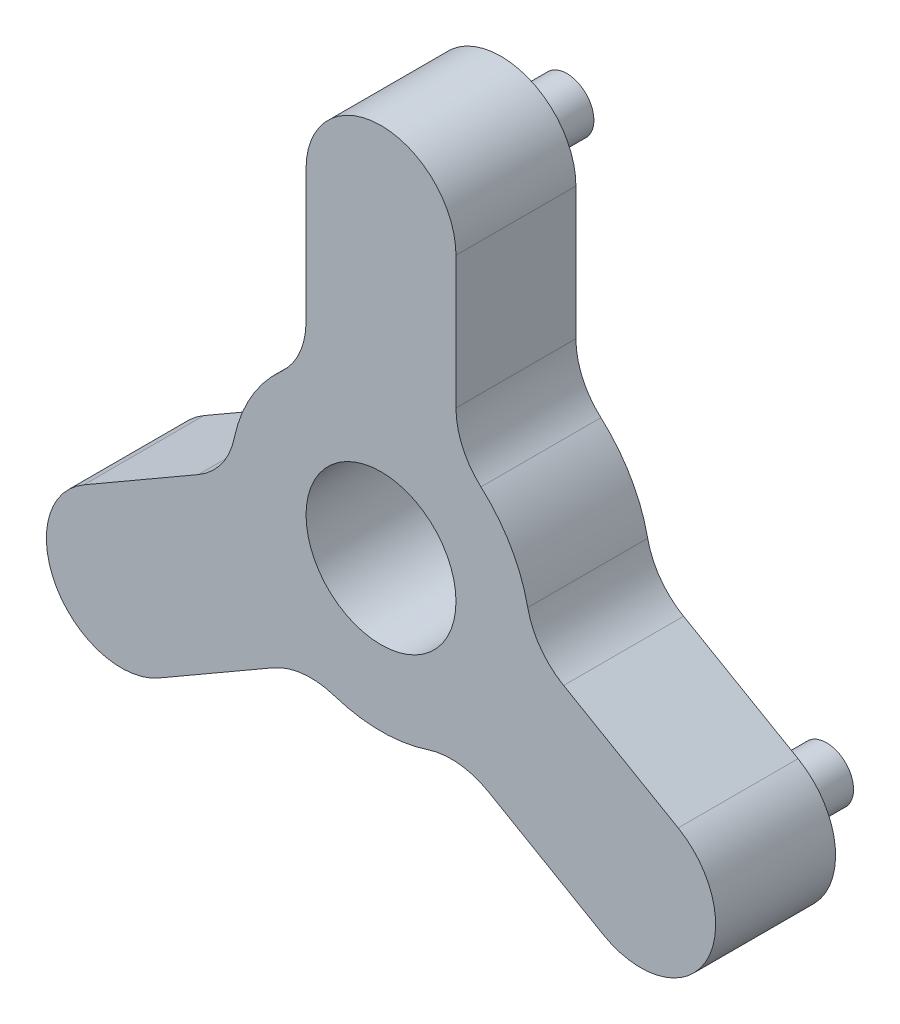
SolidWorks part; units mm, degrees
ref_plane "Front Plane" through (0, 0, 0) normal (0, 0, 1) x (1, 0, 0)
ref_plane "Top Plane" through (0, 0, 0) normal (0, 1, 0) x (1, 0, 0)
ref_plane "Right Plane" through (0, 0, 0) normal (1, 0, 0) x (0, 0, -1)
sketch "Sketch1" plane through (0, 0, 0) normal (0, 0, 1) x (1, 0, 0)
  line L0 (-6.35, 25.4) -> (-6.35, 14.199)
  line L1 (6.35, 25.4) -> (6.35, 14.199)
  line L10 (18.822, -18.1993) -> (9.1217, -12.5988)
  line L11 (25.172, -7.2007) -> (15.4717, -1.6003)
  line L12 (-25.172, -7.2007) -> (-15.4717, -1.6003)
  line L13 (-18.822, -18.1993) -> (-9.1217, -12.5988)
  circle A0 centre (0, 0) radius 25.4 construction
  circle A1 centre (0, 25.4) radius 2.2857 construction
  circle A3 centre (21.997, -12.7) radius 2.2857 construction
  arc A4 (18.822, -18.1993) -> (25.172, -7.2007) centre (21.997, -12.7) ccw
  circle A5 centre (-21.997, -12.7) radius 2.2857 construction
  arc A6 (-25.172, -7.2007) -> (-18.822, -18.1993) centre (-21.997, -12.7) ccw
  arc A7 (6.35, 25.4) -> (-6.35, 25.4) centre (0, 25.4) ccw
  arc A8 (12.4311, 2.5993) -> (8.4667, 9.466) centre (0, 0) ccw
  arc A9 (-3.9645, -12.0654) -> (3.9645, -12.0654) centre (0, 0) ccw
  arc A10 (-8.4667, 9.466) -> (-12.4311, 2.5993) centre (0, 0) ccw
  arc A11 (9.1217, -12.5988) -> (3.9645, -12.0654) centre (5.9467, -18.098) ccw
  arc A12 (-9.1217, -12.5988) -> (-3.9645, -12.0654) centre (-5.9467, -18.098) cw
  arc A13 (-15.4717, -1.6003) -> (-12.4311, 2.5993) centre (-18.6467, 3.899) ccw
  arc A14 (-6.35, 14.199) -> (-8.4667, 9.466) centre (-12.7, 14.199) cw
  arc A15 (6.35, 14.199) -> (8.4667, 9.466) centre (12.7, 14.199) ccw
  arc A16 (15.4717, -1.6003) -> (12.4311, 2.5993) centre (18.6467, 3.899) cw
  point P8 (0, 0)
  point P21 (0, 0)
  point P27 (-6.35, -10.9985)
  point P32 (-6.35, 10.9985)
  dimension "D1" = 50.8
  dimension "D2" = 4.5714
  dimension "D3" = 6.35
  dimension "D4" = 25.4
  dimension "D5" = 6.35
extrude "Boss-Extrude1" add sketch "Sketch1" along normal blind 10.16
sketch "Sketch2" plane through (0, 0, 0) normal (0, 0, -1) x (-1, 0, 0)
  circle A0 centre (0, 0) radius 25.4 construction
  circle A1 centre (0, 25.4) radius 2.2857
  circle A6 centre (21.997, -12.7) radius 2.2857
  circle A7 centre (-21.997, -12.7) radius 2.2857
  point P11 (0, 0)
  point P15 (0, 0)
  dimension "D1" = 50.8
  dimension "D2" = 4.5714
extrude "Boss-Extrude2" add sketch "Sketch2" along normal blind 5.588
sketch "Sketch3" plane through (0, 0, 0) normal (0, 0, -1) x (-1, 0, 0)
  circle A0 centre (0, 0) radius 6.35
  dimension "D1" = 12.7
extrude "Cut-Extrude1" cut sketch "Sketch3" against normal up to surface (10.16 mm away) up to face at (0, 0, 10.16)
scale "Scale1" scale about centroid uniform scaling yes scale factor 1.75
